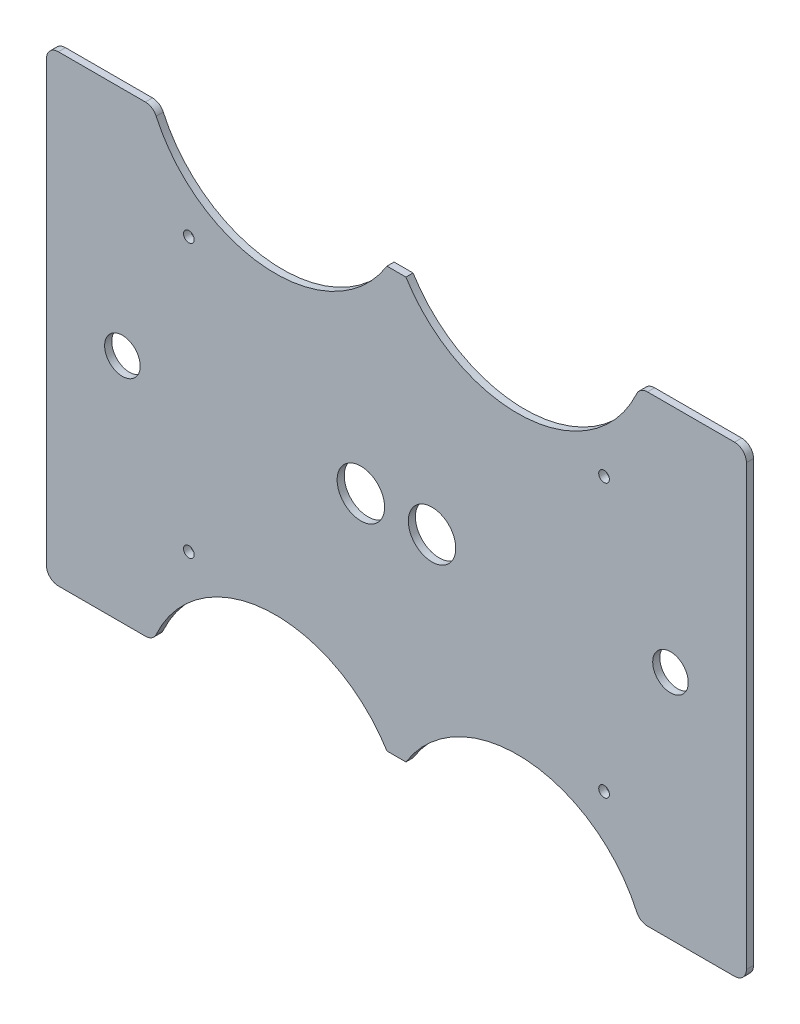
SolidWorks part; units mm, degrees
ref_plane "Plan de face" through (0, 0, 0) normal (0, 0, 1) x (1, 0, 0)
ref_plane "Plan de dessus" through (0, 0, 0) normal (0, 1, 0) x (1, 0, 0)
ref_plane "Plan de droite" through (0, 0, 0) normal (1, 0, 0) x (0, 0, -1)
sketch "Esquisse1" plane through (0, 0, 0) normal (0, 0, 1) x (1, 0, 0)
  line L0 (147.5, 48.0502) -> (147.5, -224.4935) construction
  line L1 (5, 0) -> (41.6849, 0)
  line L2 (0, -5) -> (0, -190)
  line L3 (5, -195) -> (41.6849, -195)
  line L4 (295, -5) -> (295, -190)
  line L5 (-64.1158, -97.5) -> (352.9454, -97.5) construction
  line L6 (253.3151, 0) -> (290, 0)
  line L7 (253.3151, -195) -> (290, -195)
  line L8 (151.5, -9) -> (143.5, -9)
  line L9 (151.5, -186) -> (143.5, -186)
  line L10 (32, -70.4056) -> (32, -116.3872) construction
  line L11 (132.5, -79.7871) -> (132.5, -112.487) construction
  line L12 (-23.9724, 20) -> (312.0368, 20) construction
  line L13 (96.4886, 48.0502) -> (96.4886, 6.2328) construction
  line L14 (198.5114, 48.0502) -> (198.5114, 6.2328) construction
  line L15 (162.5, -79.7871) -> (162.5, -112.487) construction
  arc A0 (143.5, -9) -> (46.234, -2.9248) centre (96.4886, 20) cw
  arc A1 (151.5, -9) -> (248.766, -2.9248) centre (198.5114, 20) ccw
  arc A2 (151.5, -186) -> (248.766, -192.0752) centre (198.5114, -215) cw
  arc A3 (143.5, -186) -> (46.234, -192.0752) centre (96.4886, -215) ccw
  circle A4 centre (60, -40) radius 2.25
  circle A5 centre (32, -97.5) radius 7.5
  circle A6 centre (263, -97.5) radius 7.5
  circle A7 centre (132.5, -97.5) radius 10
  circle A8 centre (162.5, -97.5) radius 10
  circle A10 centre (235, -40) radius 2.25
  circle A21 centre (235, -155) radius 2.25
  circle A22 centre (60, -155) radius 2.25
  arc A28 (295, -5) -> (290, 0) centre (290, -5) ccw
  arc A29 (248.766, -2.9248) -> (253.3151, 0) centre (253.3151, -5) cw
  arc A30 (46.234, -2.9248) -> (41.6849, 0) centre (41.6849, -5) ccw
  arc A31 (5, 0) -> (0, -5) centre (5, -5) ccw
  arc A32 (0, -190) -> (5, -195) centre (5, -190) ccw
  arc A33 (41.6849, -195) -> (46.234, -192.0752) centre (41.6849, -190) ccw
  arc A34 (248.766, -192.0752) -> (253.3151, -195) centre (253.3151, -190) ccw
  arc A35 (290, -195) -> (295, -190) centre (290, -190) ccw
  point P22 (147.5, -9)
  point P125 (295, 0)
  point P128 (250, 0)
  point P131 (45, 0)
  point P134 (0, 0)
  point P137 (0, -195)
  point P140 (45, -195)
  point P143 (250, -195)
  dimension "D3" = 20
  dimension "D7" = 4.5
  dimension "D10" = 32
  dimension "D13" = 20
  dimension "D24" = 5
  dimension "D25" = 5
  dimension "D26" = 5
  dimension "D27" = 5
  dimension "D28" = 5
  dimension "D29" = 5
  dimension "D30" = 5
  dimension "D31" = 5
  dimension "D11" = 15
  dimension "D12" = 15
  dimension "D1" = 295
  dimension "D2" = 195
  dimension "D4" = 45
  dimension "D5" = 4
  dimension "D6" = 9
  dimension "D8" = 60
  dimension "D9" = 40
  dimension "D16" = 51.0114
extrude "Boss.-Extru.1" add sketch "Esquisse1" along normal blind 3
